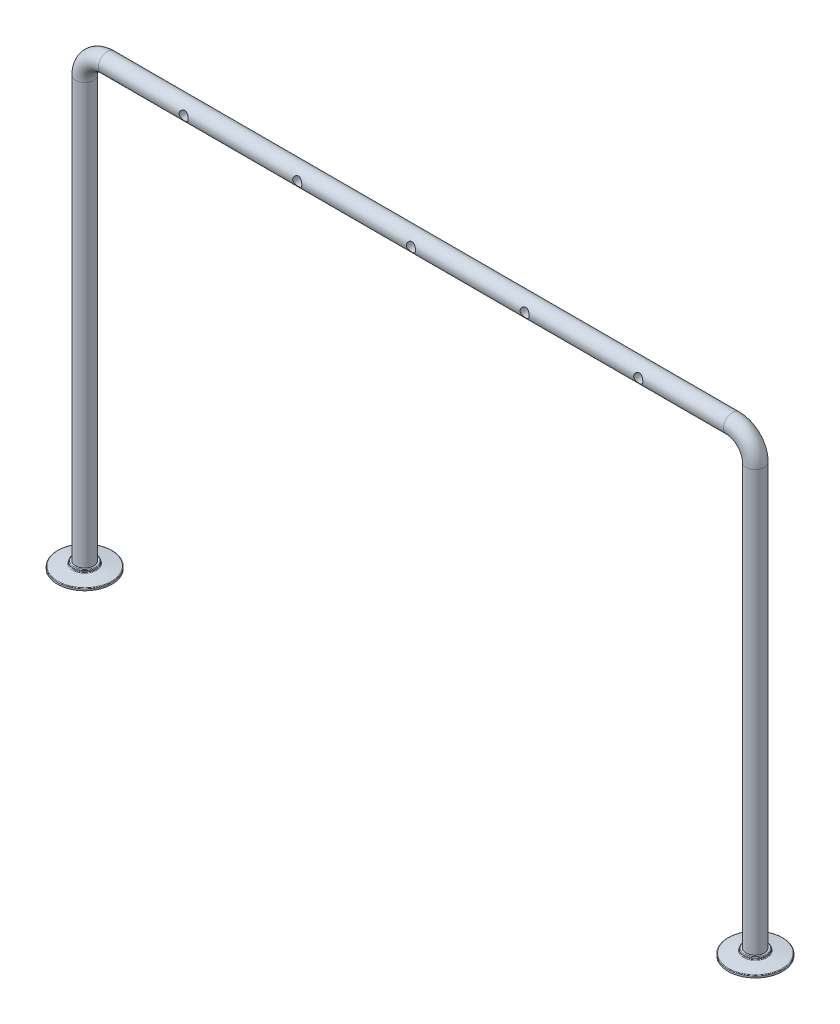
SolidWorks part; units mm, degrees
ref_plane "Front Plane" through (0, 0, 0) normal (0, 0, 1) x (1, 0, 0)
ref_plane "Top Plane" through (0, 0, 0) normal (0, 1, 0) x (1, 0, 0)
ref_plane "Right Plane" through (0, 0, 0) normal (1, 0, 0) x (0, 0, -1)
sketch "Sketch2" plane through (0, 0, 0) normal (0, 0, 1) x (1, 0, 0)
  line L0 (-147.5, -135.6134) -> (-147.5, 49.3866)
  line L1 (-137.5, 59.3866) -> (137.5, 59.3866)
  line L2 (147.5, 49.3866) -> (147.5, -135.6134)
  arc A0 (137.5, 59.3866) -> (147.5, 49.3866) centre (137.5, 49.3866) cw
  arc A1 (-147.5, 49.3866) -> (-137.5, 59.3866) centre (-137.5, 49.3866) cw
  point P2 (0, 59.3866)
  dimension "D1" = 10
  dimension "D2" = 295
  dimension "D3" = 195
  dimension "D4" = 195
sweep "Sweep1" add path "Sketch2" circular profile diameter 8 parameters "D3"=8
sketch "Sketch7" plane through (0, 0, 0) normal (0, 0, 1) x (1, 0, 0)
  line L0 (-137.5, 59.3866) -> (137.5, 59.3866) construction
  circle A0 centre (-100, 59.3866) radius 2
  circle A1 centre (-50, 59.3866) radius 2
  circle A2 centre (0, 59.3866) radius 2
  circle A3 centre (50, 59.3866) radius 2
  circle A4 centre (100, 59.3866) radius 2
  dimension "D1" = 0
  dimension "D2" = 50
  dimension "D3" = 50
  dimension "D4" = 50
  dimension "D5" = 50
  dimension "D6" = 4
  dimension "D7" = 4
  dimension "D8" = 4
  dimension "D9" = 4
  dimension "D10" = 4
extrude "Cut-Extrude1" cut sketch "Sketch7" along normal through all from surface at 0 starting at plane "Front Plane"
sketch "Sketch8" plane through (0, 0, 0) normal (0, 0, 1) x (1, 0, 0)
  line L0 (-147.5, -135.6134) -> (-152.2, -135.6134)
  line L1 (-151.5, -135.6134) -> (-143.5, -135.6134) construction
  line L2 (-152.5, -135.9134) -> (-152.5, -136.3532)
  line L3 (-152.7576, -136.6502) -> (-159.2424, -137.5766)
  line L4 (-159.5, -137.8736) -> (-159.5, -138.6134)
  line L5 (-159.5, -138.6134) -> (-147.5, -138.6134)
  line L6 (-147.5, -135.6134) -> (-147.5, 49.3866) construction
  line L7 (-147.5, -138.6134) -> (-147.5, -135.6134)
  arc A0 (-152.2, -135.6134) -> (-152.5, -135.9134) centre (-152.2, -135.9134) ccw
  arc A1 (-152.5, -136.3532) -> (-152.7576, -136.6502) centre (-152.8, -136.3532) cw
  arc A2 (-159.2424, -137.5766) -> (-159.5, -137.8736) centre (-159.2, -137.8736) ccw
  point P12 (-152.5, -135.6134)
  point P15 (-152.5, -136.6134)
  point P18 (-159.5, -137.6134)
  dimension "D6" = 0.3
  dimension "D1" = 5
  dimension "D2" = 12
  dimension "D3" = 1
  dimension "D4" = 1
  dimension "D5" = 3
revolve "Revolve1" add sketch "Sketch8" angle 360 about L7
mirror "Mirror1" about plane through (0, 0, 0) normal (1, 0, 0) of "Revolve1"
